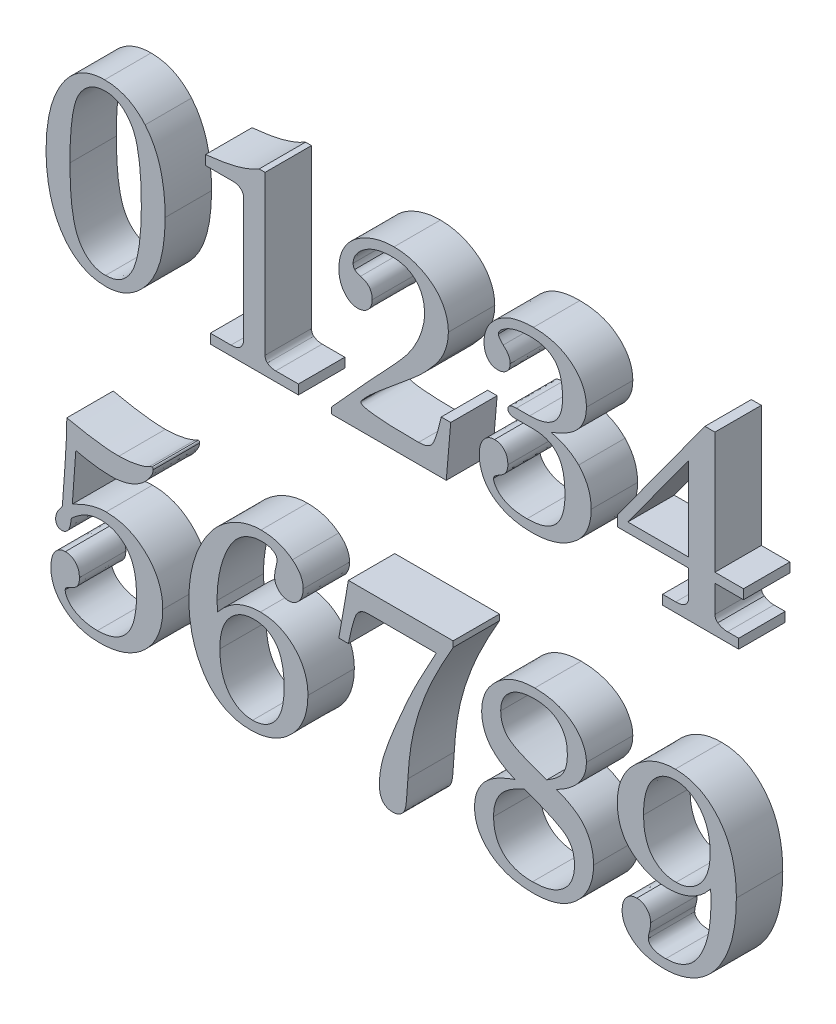
SolidWorks part; units mm, degrees
ref_plane "Plan de face" through (0, 0, 0) normal (0, 0, 1) x (1, 0, 0)
ref_plane "Plan de dessus" through (0, 0, 0) normal (0, 1, 0) x (1, 0, 0)
ref_plane "Plan de droite" through (0, 0, 0) normal (1, 0, 0) x (0, 0, -1)
sketch "Esquisse1" plane through (0, 0, 0) normal (0, 0, 1) x (1, 0, 0)
  text T0 "01234\r\n56789" font "Century Schoolbook" height 40
extrude "Boss.-Extru.1" add sketch "Esquisse1" along normal blind 10
